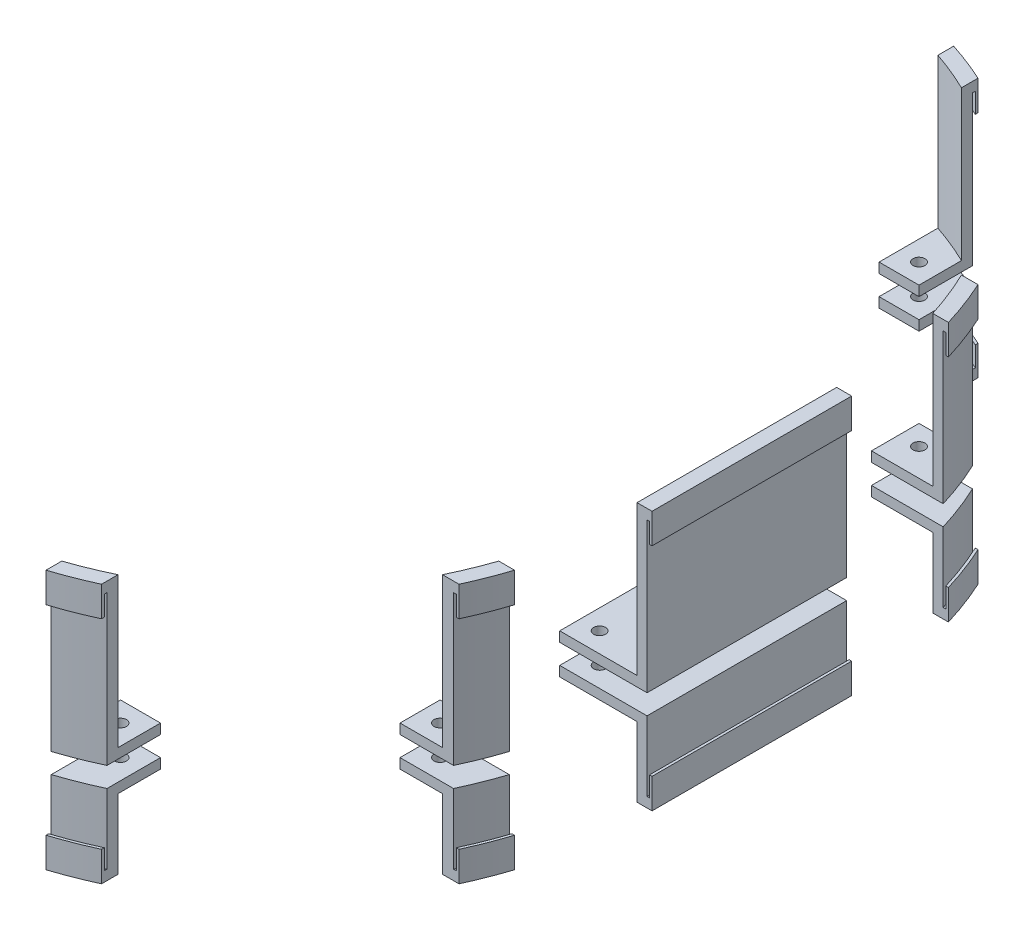
SolidWorks part; units mm, degrees
ref_plane "Front Plane" through (0, 0, 0) normal (0, 0, 1) x (1, 0, 0)
ref_plane "Top Plane" through (0, 0, 0) normal (0, 1, 0) x (1, 0, 0)
ref_plane "Right Plane" through (0, 0, 0) normal (1, 0, 0) x (0, 0, -1)
sketch "Sketch1" plane through (0, 0, 0) normal (0, 1, 0) x (1, 0, 0)
  line L1 (-34.1312, -148.4312) -> (34.1313, -148.4312)
  line L2 (-148.4312, -34.1312) -> (-148.4312, 34.1313)
  line L3 (-34.1312, 148.4313) -> (34.1313, 148.4313)
  line L4 (148.4312, -34.1312) -> (148.4312, 34.1313)
  line L5 (-148.4312, -148.4312) -> (148.4313, 148.4312) construction
  line L6 (-148.4312, 148.4312) -> (148.4313, -148.4312) construction
  arc A1 (-34.1312, -148.4312) -> (-148.4312, -34.1312) centre (-34.1312, -34.1312) cw
  arc A2 (34.1313, -148.4312) -> (148.4312, -34.1312) centre (34.1313, -34.1312) ccw
  arc A3 (34.1313, 148.4313) -> (148.4312, 34.1313) centre (34.1313, 34.1313) cw
  arc A4 (-148.4312, 34.1313) -> (-34.1312, 148.4313) centre (-34.1312, 34.1313) cw
  point P0 (0, 0)
  dimension "D1" = 296.8625
  dimension "D3" = 114.3
  dimension "D2" = 296.8625
extrude "Boss-Extrude1" add sketch "Sketch1" along normal blind 6.35
sketch "Sketch4" plane through (0, 6.35, 0) normal (0, 1, 0) x (1, 0, 0)
  line L0 (-39.448, -144.217) -> (39.448, -144.217)
  line L1 (-39.448, -120.2902) -> (39.448, -120.2902)
  line L2 (-39.448, 120.2902) -> (39.448, 120.2902)
  line L3 (-39.448, 144.217) -> (39.448, 144.217)
  line L4 (-39.448, 118.7027) -> (39.448, 118.7027)
  line L5 (-39.448, 145.8045) -> (39.448, 145.8045)
  line L6 (-39.448, -145.8045) -> (39.448, -145.8045)
  line L7 (-39.448, -118.7027) -> (39.448, -118.7027)
  line L8 (-13.125, 107.0625) -> (-13.125, 100.3125) construction
  line L9 (-13.125, 100.3125) -> (-18.875, 100.3125) construction
  line L10 (-18.875, 100.3125) -> (-18.875, 107.0625) construction
  line L11 (-18.875, 107.0625) -> (-13.125, 107.0625) construction
  line L12 (18.875, 107.0625) -> (18.875, 100.3125) construction
  line L13 (18.875, 100.3125) -> (13.125, 100.3125) construction
  line L14 (13.125, 100.3125) -> (13.125, 107.0625) construction
  line L15 (13.125, 107.0625) -> (18.875, 107.0625) construction
  line L16 (-7, 56.325) -> (-13, 56.325) construction
  line L17 (-13, 56.325) -> (-13, 64.325) construction
  line L18 (-13, 64.325) -> (-7, 64.325) construction
  line L19 (-7, 64.325) -> (-7, 56.325) construction
  line L20 (25, 56.325) -> (19, 56.325) construction
  line L21 (19, 56.325) -> (19, 64.325) construction
  line L22 (19, 64.325) -> (25, 64.325) construction
  line L23 (25, 64.325) -> (25, 56.325) construction
  line L24 (-13, -56.325) -> (-7, -56.325) construction
  line L25 (-7, -56.325) -> (-7, -64.325) construction
  line L26 (-7, -64.325) -> (-13, -64.325) construction
  line L27 (-13, -64.325) -> (-13, -56.325) construction
  line L28 (19, -56.325) -> (25, -56.325) construction
  line L29 (25, -56.325) -> (25, -64.325) construction
  line L30 (25, -64.325) -> (19, -64.325) construction
  line L31 (19, -64.325) -> (19, -56.325) construction
  line L32 (-18.875, -107.0625) -> (-18.875, -100.3125) construction
  line L33 (-18.875, -100.3125) -> (-13.125, -100.3125) construction
  line L34 (-13.125, -100.3125) -> (-13.125, -107.0625) construction
  line L35 (-13.125, -107.0625) -> (-18.875, -107.0625) construction
  line L36 (13.125, -107.0625) -> (13.125, -100.3125) construction
  line L37 (13.125, -100.3125) -> (18.875, -100.3125) construction
  line L38 (18.875, -100.3125) -> (18.875, -107.0625) construction
  line L39 (18.875, -107.0625) -> (13.125, -107.0625) construction
  line L40 (-13.125, 107.0625) -> (-13.125, 100.3125)
  line L41 (-13.125, 100.3125) -> (-18.875, 100.3125)
  line L42 (-18.875, 100.3125) -> (-18.875, 107.0625)
  line L43 (-18.875, 107.0625) -> (-13.125, 107.0625)
  line L44 (18.875, 107.0625) -> (18.875, 100.3125)
  line L45 (18.875, 100.3125) -> (13.125, 100.3125)
  line L46 (13.125, 100.3125) -> (13.125, 107.0625)
  line L47 (13.125, 107.0625) -> (18.875, 107.0625)
  line L48 (-7, 56.325) -> (-13, 56.325)
  line L49 (-13, 56.325) -> (-13, 64.325)
  line L50 (-13, 64.325) -> (-7, 64.325)
  line L51 (-7, 64.325) -> (-7, 56.325)
  line L52 (25, 56.325) -> (19, 56.325)
  line L53 (19, 56.325) -> (19, 64.325)
  line L54 (19, 64.325) -> (25, 64.325)
  line L55 (25, 64.325) -> (25, 56.325)
  line L56 (-13, -56.325) -> (-7, -56.325)
  line L57 (-7, -56.325) -> (-7, -64.325)
  line L58 (-7, -64.325) -> (-13, -64.325)
  line L59 (-13, -64.325) -> (-13, -56.325)
  line L60 (19, -56.325) -> (25, -56.325)
  line L61 (25, -56.325) -> (25, -64.325)
  line L62 (25, -64.325) -> (19, -64.325)
  line L63 (19, -64.325) -> (19, -56.325)
  line L64 (-18.875, -107.0625) -> (-18.875, -100.3125)
  line L65 (-18.875, -100.3125) -> (-13.125, -100.3125)
  line L66 (-13.125, -100.3125) -> (-13.125, -107.0625)
  line L67 (-13.125, -107.0625) -> (-18.875, -107.0625)
  line L68 (13.125, -107.0625) -> (13.125, -100.3125)
  line L69 (13.125, -100.3125) -> (18.875, -100.3125)
  line L70 (18.875, -100.3125) -> (18.875, -107.0625)
  line L71 (18.875, -107.0625) -> (13.125, -107.0625)
  line L72 (-18.875, -107.0625) -> (-13.125, -100.3125) construction
  line L73 (13.125, -107.0625) -> (18.875, -100.3125) construction
  line L74 (-13, -64.325) -> (-7, -56.325) construction
  line L75 (19, -64.325) -> (25, -56.325) construction
  line L76 (-13, 56.325) -> (-7, 64.325) construction
  line L77 (19, 56.325) -> (25, 64.325) construction
  line L78 (13.125, 100.3125) -> (18.875, 107.0625) construction
  line L79 (-18.875, 100.3125) -> (-13.125, 107.0625) construction
  arc A0 (58.6792, -125.8296) -> (39.448, -120.2902) centre (39.448, -156.4424) ccw construction
  arc A1 (58.6792, -138.6776) -> (58.6792, -125.8296) centre (54.6436, -132.2536) ccw construction
  arc A2 (39.448, -144.217) -> (58.6792, -138.6776) centre (39.448, -108.0647) ccw construction
  arc A3 (-39.448, -120.2902) -> (-58.6792, -125.8296) centre (-39.448, -156.4424) ccw construction
  arc A4 (-58.6792, -125.8296) -> (-58.6792, -138.6776) centre (-54.6436, -132.2536) ccw construction
  arc A5 (-58.6792, -138.6776) -> (-39.448, -144.217) centre (-39.448, -108.0647) ccw construction
  arc A6 (-58.6792, 125.8296) -> (-39.448, 120.2902) centre (-39.448, 156.4424) ccw construction
  arc A7 (-58.6792, 138.6776) -> (-58.6792, 125.8296) centre (-54.6436, 132.2536) ccw construction
  arc A8 (-39.448, 144.217) -> (-58.6792, 138.6776) centre (-39.448, 108.0647) ccw construction
  arc A9 (58.6792, 138.6776) -> (39.448, 144.217) centre (39.448, 108.0647) ccw construction
  arc A10 (58.6792, 125.8296) -> (58.6792, 138.6776) centre (54.6436, 132.2536) ccw construction
  arc A11 (39.448, 120.2902) -> (58.6792, 125.8296) centre (39.448, 156.4424) ccw construction
  arc A12 (58.6792, -125.8296) -> (39.448, -120.2902) centre (39.448, -156.4424) ccw
  arc A13 (58.6792, -138.6776) -> (58.6792, -125.8296) centre (54.6436, -132.2536) ccw
  arc A14 (39.448, -144.217) -> (58.6792, -138.6776) centre (39.448, -108.0647) ccw
  arc A15 (-39.448, -120.2902) -> (-58.6792, -125.8296) centre (-39.448, -156.4424) ccw
  arc A16 (-58.6792, -125.8296) -> (-58.6792, -138.6776) centre (-54.6436, -132.2536) ccw
  arc A17 (-58.6792, -138.6776) -> (-39.448, -144.217) centre (-39.448, -108.0647) ccw
  arc A18 (-58.6792, 125.8296) -> (-39.448, 120.2902) centre (-39.448, 156.4424) ccw
  arc A19 (-58.6792, 138.6776) -> (-58.6792, 125.8296) centre (-54.6436, 132.2536) ccw
  arc A20 (-39.448, 144.217) -> (-58.6792, 138.6776) centre (-39.448, 108.0647) ccw
  arc A21 (58.6792, 138.6776) -> (39.448, 144.217) centre (39.448, 108.0647) ccw
  arc A22 (58.6792, 125.8296) -> (58.6792, 138.6776) centre (54.6436, 132.2536) ccw
  arc A23 (39.448, 120.2902) -> (58.6792, 125.8296) centre (39.448, 156.4424) ccw
  arc A24 (-59.5236, 124.4853) -> (-39.448, 118.7027) centre (-39.448, 156.4424) ccw
  arc A25 (39.448, 118.7027) -> (59.5236, 124.4853) centre (39.448, 156.4424) ccw
  arc A26 (59.5236, 124.4853) -> (59.5236, 140.0219) centre (54.6436, 132.2536) ccw
  arc A27 (59.5236, 140.0219) -> (39.448, 145.8045) centre (39.448, 108.0647) ccw
  arc A28 (-39.448, 145.8045) -> (-59.5236, 140.0219) centre (-39.448, 108.0647) ccw
  arc A29 (-59.5236, 140.0219) -> (-59.5236, 124.4853) centre (-54.6436, 132.2536) ccw
  arc A30 (39.448, -145.8045) -> (59.5236, -140.0219) centre (39.448, -108.0647) ccw
  arc A31 (59.5236, -140.0219) -> (59.5236, -124.4853) centre (54.6436, -132.2536) ccw
  arc A32 (59.5236, -124.4853) -> (39.448, -118.7027) centre (39.448, -156.4424) ccw
  arc A33 (-39.448, -118.7027) -> (-59.5236, -124.4853) centre (-39.448, -156.4424) ccw
  arc A34 (-59.5236, -124.4853) -> (-59.5236, -140.0219) centre (-54.6436, -132.2536) ccw
  arc A35 (-59.5236, -140.0219) -> (-39.448, -145.8045) centre (-39.448, -108.0647) ccw
  point P58 (-16, -103.6875)
  point P60 (16, 103.6875)
  point P62 (-16, 103.6875)
  point P63 (-10, 60.325)
  point P66 (22, 60.325)
  point P68 (-10, -60.325)
  point P70 (16, -103.6875)
  point P71 (22, -60.325)
  dimension "D1" = 1.5875
extrude "Cut-Extrude1" cut sketch "Sketch4" against normal blind 6.35 contours L2 A23 A22 A21 L3 A20 A19 A18 | A28 A29 A24 L4 A25 A26 A27 L5 A23 L2 A18 A19 A20 L3 A21 A22 | A16 A17 L0 A14 A13 A12 L1 A15 | A34 A35 L6 A30 A31 A32 L7 A33 A17 A16 A15 L1 A12 A13 A14 L0
hole_wizard "M4 Clearance Hole1" positions "Sketch7" profile "Sketch9" hole size "M4" standard "ANSI Metric" end condition through all
sketch "Sketch7" plane through (0, 6.35, 0) normal (0, 1, 0) x (1, 0, 0)
  point P0 (-16, -103.6875)
  point P3 (16, -103.6875)
  point P6 (22, -60.325)
  point P9 (-10, -60.325)
  point P12 (-10, 60.325)
  point P15 (22, 60.325)
  point P18 (16, 103.6875)
  point P21 (-16, 103.6875)
sketch "Sketch9" plane through (-16, 6.35, 103.6875) normal (1, 0, 0) x (0, 0, 1)
  line L0 (0, 0) -> (0, 6.35)
  line L1 (0, 6.35) -> (2.25, 6.35)
  line L2 (2.25, 6.35) -> (2.25, 0)
  line L5 (2.25, 0) -> (0, 0)
  line L11 (0, -6.35) -> (0, 107.95) construction
  dimension "Thru Hole Dia." = 4.5
  dimension "Thru Hole Depth" = 6.35
sketch "Sketch11" plane through (0, 6.35, 0) normal (0, 1, 0) x (1, 0, 0)
  line L1 (101.6, 101.6) -> (-101.6, 101.6)
  line L2 (101.6, 101.6) -> (101.6, -101.6)
  line L3 (101.6, -101.6) -> (-101.6, -101.6)
  line L4 (-101.6, 101.6) -> (-101.6, -101.6)
  line L5 (101.6, 101.6) -> (-101.6, -101.6) construction
  line L6 (101.6, -101.6) -> (-101.6, 101.6) construction
  circle A0 centre (0, 0) radius 143.6841 construction
  point P7 (-127, -101.6)
  point P10 (-127, 101.6)
  point P11 (-127, -76.2)
  point P12 (-127, -50.8)
  point P13 (-127, -25.4)
  point P14 (-127, 0)
  point P15 (-127, 25.4)
  point P16 (-127, 50.8)
  point P17 (-127, 76.2)
  point P18 (-101.6, -101.6)
  point P19 (-101.6, 101.6)
  point P20 (-101.6, -76.2)
  point P21 (-101.6, -50.8)
  point P22 (-101.6, -25.4)
  point P23 (-101.6, 0)
  point P24 (-101.6, 25.4)
  point P25 (-101.6, 50.8)
  point P26 (-101.6, 76.2)
  point P27 (-76.2, -101.6)
  point P28 (-76.2, 101.6)
  point P29 (-76.2, -76.2)
  point P30 (-76.2, -50.8)
  point P31 (-76.2, -25.4)
  point P32 (-76.2, 0)
  point P33 (-76.2, 25.4)
  point P34 (-76.2, 50.8)
  point P35 (-76.2, 76.2)
  point P36 (-50.8, -101.6)
  point P37 (-50.8, 101.6)
  point P38 (-50.8, -76.2)
  point P39 (-50.8, -50.8)
  point P40 (-50.8, -25.4)
  point P41 (-50.8, 0)
  point P42 (-50.8, 25.4)
  point P43 (-50.8, 50.8)
  point P44 (-50.8, 76.2)
  point P45 (-25.4, -101.6)
  point P46 (-25.4, 101.6)
  point P47 (-25.4, -76.2)
  point P48 (-25.4, -50.8)
  point P49 (-25.4, -25.4)
  point P50 (-25.4, 0)
  point P51 (-25.4, 25.4)
  point P52 (-25.4, 50.8)
  point P53 (-25.4, 76.2)
  point P54 (0, -101.6)
  point P55 (0, 101.6)
  point P56 (0, -76.2)
  point P57 (0, -50.8)
  point P58 (0, -25.4)
  point P59 (0, 0)
  point P60 (0, 25.4)
  point P61 (0, 50.8)
  point P62 (0, 76.2)
  point P63 (25.4, -101.6)
  point P64 (25.4, 101.6)
  point P65 (25.4, -76.2)
  point P66 (25.4, -50.8)
  point P67 (25.4, -25.4)
  point P68 (25.4, 0)
  point P69 (25.4, 25.4)
  point P70 (25.4, 50.8)
  point P71 (25.4, 76.2)
  point P72 (50.8, -101.6)
  point P73 (50.8, 101.6)
  point P74 (50.8, -76.2)
  point P75 (50.8, -50.8)
  point P76 (50.8, -25.4)
  point P77 (50.8, 0)
  point P78 (50.8, 25.4)
  point P79 (50.8, 50.8)
  point P80 (50.8, 76.2)
  point P81 (76.2, -101.6)
  point P82 (76.2, 101.6)
  point P83 (76.2, -76.2)
  point P84 (76.2, -50.8)
  point P85 (76.2, -25.4)
  point P86 (76.2, 0)
  point P87 (76.2, 25.4)
  point P88 (76.2, 50.8)
  point P89 (76.2, 76.2)
  point P90 (101.6, -101.6)
  point P91 (101.6, 101.6)
  point P92 (101.6, -76.2)
  point P93 (101.6, -50.8)
  point P94 (101.6, -25.4)
  point P95 (101.6, 0)
  point P96 (101.6, 25.4)
  point P97 (101.6, 50.8)
  point P98 (101.6, 76.2)
  point P99 (127, -101.6)
  point P100 (127, 101.6)
  point P101 (127, -76.2)
  point P102 (127, -50.8)
  point P103 (127, -25.4)
  point P104 (127, 0)
  point P105 (127, 25.4)
  point P106 (127, 50.8)
  point P107 (127, 76.2)
  dimension "D1" = 203.2
  dimension "D2" = 25.4
  dimension "D3" = 11
  dimension "D4" = 9
hole_wizard "#6 Clearance Hole1" positions "Sketch12" profile "Sketch13" hole size "#6" standard "ANSI Inch" end condition through all
sketch "Sketch12" plane through (0, 6.35, 0) normal (0, 1, 0) x (1, 0, 0)
  point P0 (-101.6, -101.6)
  point P3 (-101.6, 101.6)
  point P6 (101.6, 101.6)
  point P9 (101.6, -101.6)
  point P12 (-127, -76.2)
  point P15 (-127, -50.8)
  point P18 (-127, 50.8)
  point P21 (-127, 76.2)
  point P24 (-101.6, 76.2)
  point P27 (-101.6, 50.8)
  point P30 (-101.6, 25.4)
  point P33 (-101.6, 0)
  point P36 (-101.6, -25.4)
  point P39 (-101.6, -50.8)
  point P42 (-101.6, -76.2)
  point P45 (-76.2, -101.6)
  point P48 (-50.8, -101.6)
  point P51 (-50.8, -76.2)
  point P54 (-76.2, -76.2)
  point P57 (-76.2, -50.8)
  point P60 (-50.8, -50.8)
  point P63 (-50.8, -25.4)
  point P66 (-76.2, -25.4)
  point P69 (-76.2, 0)
  point P72 (-50.8, 0)
  point P75 (-50.8, 25.4)
  point P78 (-76.2, 25.4)
  point P81 (-76.2, 50.8)
  point P84 (-50.8, 50.8)
  point P87 (-50.8, 76.2)
  point P90 (-76.2, 76.2)
  point P93 (-76.2, 101.6)
  point P96 (-50.8, 101.6)
  point P99 (50.8, -101.6)
  point P102 (76.2, -101.6)
  point P105 (101.6, -76.2)
  point P108 (127, -76.2)
  point P111 (127, -50.8)
  point P114 (101.6, -25.4)
  point P117 (101.6, -50.8)
  point P120 (76.2, -25.4)
  point P123 (76.2, -50.8)
  point P126 (76.2, -76.2)
  point P129 (50.8, -76.2)
  point P132 (50.8, -50.8)
  point P135 (50.8, -25.4)
  point P138 (50.8, 0)
  point P141 (76.2, 0)
  point P144 (101.6, 0)
  point P147 (101.6, 25.4)
  point P150 (101.6, 50.8)
  point P153 (101.6, 76.2)
  point P156 (127, 50.8)
  point P159 (127, 76.2)
  point P162 (76.2, 101.6)
  point P165 (50.8, 101.6)
  point P168 (50.8, 76.2)
  point P171 (76.2, 76.2)
  point P174 (76.2, 50.8)
  point P177 (76.2, 25.4)
  point P180 (50.8, 25.4)
  point P183 (50.8, 50.8)
  point P186 (0, 0)
  point P189 (-25.4, -25.4)
  point P192 (-25.4, 0)
  point P195 (-25.4, 25.4)
  point P198 (0, 25.4)
  point P201 (25.4, 25.4)
  point P204 (25.4, 0)
  point P207 (25.4, -25.4)
  point P210 (0, -25.4)
  point P213 (127, -25.4)
  point P216 (127, 0)
  point P219 (127, 25.4)
  point P222 (-127, -25.4)
  point P225 (-127, 0)
  point P228 (-127, 25.4)
sketch "Sketch13" plane through (-101.6, 6.35, 101.6) normal (1, 0, 0) x (0, 0, 1)
  line L0 (0, 0) -> (0, 6.35)
  line L1 (0, 6.35) -> (1.8986, 6.35)
  line L2 (1.8986, 6.35) -> (1.8986, 0)
  line L5 (1.8986, 0) -> (0, 0)
  line L11 (0, -6.35) -> (0, 107.95) construction
  dimension "Thru Hole Dia." = 3.7973
  dimension "Thru Hole Depth" = 6.35
sketch "Sketch14" plane through (0, 6.35, 0) normal (0, 1, 0) x (1, 0, 0)
  line L1 (76.2, -127) -> (-76.2, -127)
  line L2 (76.2, -127) -> (76.2, 127)
  line L3 (76.2, 127) -> (-76.2, 127)
  line L4 (-76.2, -127) -> (-76.2, 127)
  line L5 (76.2, -127) -> (-76.2, 127) construction
  line L6 (76.2, 127) -> (-76.2, -127) construction
  circle A1 centre (-76.2, -101.6) radius 1.8986 construction
  circle A2 centre (-101.6, -101.6) radius 1.8986 construction
  point P0 (0, 0)
  dimension "D1" = 25.4
  dimension "D2" = 25.4
hole_wizard "#6 Clearance Hole2" positions "Sketch15" profile "Sketch16" hole size "#6" standard "ANSI Inch" end condition through all
sketch "Sketch15" plane through (0, 6.35, 0) normal (0, 1, 0) x (1, 0, 0)
  point P0 (-76.2, -127)
  point P3 (76.2, -127)
  point P6 (76.2, 127)
  point P9 (-76.2, 127)
sketch "Sketch16" plane through (-76.2, 6.35, 127) normal (1, 0, 0) x (0, 0, 1)
  line L0 (0, 0) -> (0, 6.35)
  line L1 (0, 6.35) -> (1.8986, 6.35)
  line L2 (1.8986, 6.35) -> (1.8986, 0)
  line L5 (1.8986, 0) -> (0, 0)
  line L11 (0, -6.35) -> (0, 107.95) construction
  dimension "Thru Hole Dia." = 3.7973
  dimension "Thru Hole Depth" = 6.35
sketch "Sketch17" plane through (0, 6.35, 0) normal (0, 1, 0) x (1, 0, 0)
  line L0 (148.4313, -34.1312) -> (148.4312, 34.1313) construction
  line L1 (148.4313, -34.1312) -> (148.4312, 34.1313)
  line L2 (143.4746, 67.4257) -> (120.65, 67.4257)
  line L3 (148.4312, -31.75) -> (120.65, -31.75)
  line L4 (148.4312, -31.75) -> (148.4312, 31.75)
  line L5 (148.4312, 31.75) -> (120.65, 31.75)
  line L6 (120.65, -31.75) -> (120.65, 31.75)
  line L7 (120.65, 67.4257) -> (120.65, 82.55)
  line L8 (120.65, 82.55) -> (137.6692, 82.55)
  line L9 (82.55, 120.65) -> (69.85, 120.65)
  line L10 (69.85, 120.65) -> (69.85, 142.7068)
  line L11 (82.55, 120.65) -> (82.55, 137.6692)
  line L12 (69.85, -142.7068) -> (69.85, -120.65)
  line L13 (69.85, -120.65) -> (82.55, -120.65)
  line L14 (82.55, -120.65) -> (82.55, -137.6692)
  line L15 (137.6692, -82.55) -> (120.65, -82.55)
  line L16 (120.65, -82.55) -> (120.65, -69.85)
  line L17 (120.65, -69.85) -> (142.7068, -69.85)
  line L26 (-148.4312, 34.1313) -> (-148.4312, -34.1312)
  line L27 (34.1313, 148.4313) -> (-34.1312, 148.4313)
  line L28 (148.4313, -34.1312) -> (148.4312, 34.1313)
  line L29 (-34.1312, -148.4312) -> (34.1313, -148.4312)
  line L30 (-148.4312, 34.1313) -> (-148.4312, -34.1312)
  line L31 (34.1313, 148.4313) -> (-34.1312, 148.4313)
  line L32 (148.4313, -34.1312) -> (148.4312, 34.1313)
  line L33 (-34.1312, -148.4312) -> (34.1313, -148.4312)
  circle A0 centre (76.2, 127) radius 1.8987 construction
  circle A1 centre (127, 76.2) radius 1.8987 construction
  circle A2 centre (127, 0) radius 1.8986 construction
  circle A3 centre (127, 25.4) radius 1.8987 construction
  circle A4 centre (127, -25.4) radius 1.8986 construction
  circle A5 centre (127, -76.2) radius 1.8986 construction
  circle A6 centre (76.2, -127) radius 1.8987 construction
  arc A7 (148.4312, 34.1313) -> (34.1313, 148.4313) centre (34.1313, 34.1313) ccw construction
  arc A8 (34.1313, -148.4312) -> (148.4313, -34.1312) centre (34.1313, -34.1312) ccw construction
  circle A9 centre (76.2, 127) radius 1.8987
  circle A10 centre (127, 76.2) radius 1.8987
  circle A11 centre (127, 0) radius 1.8986
  circle A12 centre (127, 25.4) radius 1.8987
  circle A13 centre (127, -25.4) radius 1.8986
  circle A14 centre (127, -76.2) radius 1.8986
  circle A15 centre (76.2, -127) radius 1.8987
  arc A16 (143.4746, 67.4257) -> (137.6692, 82.55) centre (34.1313, 34.1313) ccw
  arc A17 (69.85, -142.7068) -> (82.55, -137.6692) centre (34.1313, -34.1312) ccw
  arc A18 (137.6692, -82.55) -> (142.7068, -69.85) centre (34.1313, -34.1312) ccw
  arc A19 (82.55, 137.6692) -> (69.85, 142.7068) centre (34.1313, 34.1313) ccw
  arc A28 (-148.4312, -34.1312) -> (-34.1312, -148.4312) centre (-34.1312, -34.1312) ccw
  arc A29 (-34.1312, 148.4313) -> (-148.4312, 34.1313) centre (-34.1312, 34.1313) ccw
  arc A30 (148.4312, 34.1313) -> (34.1313, 148.4313) centre (34.1313, 34.1313) ccw
  arc A31 (34.1313, -148.4312) -> (148.4313, -34.1312) centre (34.1313, -34.1312) ccw
  arc A32 (-148.4312, -34.1312) -> (-34.1312, -148.4312) centre (-34.1312, -34.1312) ccw
  arc A33 (-34.1312, 148.4313) -> (-148.4312, 34.1313) centre (-34.1312, 34.1313) ccw
  arc A34 (148.4312, 34.1313) -> (34.1313, 148.4313) centre (34.1313, 34.1313) ccw
  arc A35 (34.1313, -148.4312) -> (148.4313, -34.1312) centre (34.1313, -34.1312) ccw
  dimension "D1" = 6.35
  dimension "D2" = 6.35
  dimension "D3" = 6.35
  dimension "D4" = 6.35
  dimension "D5" = 6.35
  dimension "D6" = 6.35
  dimension "D7" = 6.35
  dimension "D8" = 6.35
  dimension "D9" = 6.35
  dimension "D10" = 6.35
  dimension "D11" = 6.35
  dimension "D12" = 8.7743
  dimension "D13" = 6.35
  dimension "D14" = 6.35
  dimension "D15" = 6.35
  dimension "D16" = 0
sketch "Sketch18" plane through (0, 0, 0) normal (0, -1, 0) x (1, 0, 0)
  line L4 (-148.4312, 34.1312) -> (-148.4312, -34.1312)
  line L5 (-34.1312, -148.4313) -> (34.1313, -148.4313)
  line L6 (148.4313, -34.1313) -> (148.4313, 34.1312)
  line L7 (34.1313, 148.4312) -> (-34.1312, 148.4312)
  line L8 (-148.4312, 34.1312) -> (-148.4312, -34.1312)
  line L9 (-34.1312, -148.4313) -> (34.1313, -148.4313)
  line L10 (148.4313, -34.1313) -> (148.4313, 34.1312)
  line L11 (34.1313, 148.4312) -> (-34.1312, 148.4312)
  arc A4 (-34.1312, 148.4312) -> (-148.4312, 34.1312) centre (-34.1312, 34.1312) ccw
  arc A5 (-148.4312, -34.1312) -> (-34.1312, -148.4313) centre (-34.1312, -34.1313) ccw
  arc A6 (34.1313, -148.4313) -> (148.4313, -34.1313) centre (34.1313, -34.1313) ccw
  arc A7 (148.4313, 34.1312) -> (34.1313, 148.4312) centre (34.1313, 34.1312) ccw
  arc A8 (-34.1312, 148.4312) -> (-148.4312, 34.1312) centre (-34.1312, 34.1312) ccw
  arc A9 (-148.4312, -34.1312) -> (-34.1312, -148.4313) centre (-34.1312, -34.1313) ccw
  arc A10 (34.1313, -148.4313) -> (148.4313, -34.1313) centre (34.1313, -34.1313) ccw
  arc A11 (148.4313, 34.1312) -> (34.1313, 148.4312) centre (34.1313, 34.1312) ccw
  dimension "D1" = 0
extrude "Boss-Extrude2" add sketch "Sketch17" along normal blind 3.175 contours L12 A17 L14 L13 A15 | L15 A18 L17 L16 A14 | L6 L3 L1 L5 A13 A12 A11 | L2 A16 L8 L7 A10 | L11 A19 L10 L9 A9
ref_plane "Plane1" through (0, 3.175, 0) normal (0, 1, 0) x (1, 0, 0)
mirror "Mirror3" about plane through (0, 3.175, 0) normal (0, 1, 0) of "Boss-Extrude2"
extrude "Cut-Extrude4" cut sketch "Sketch18" against normal blind 6.35
sketch "Sketch19" plane through (0, 9.525, 0) normal (0, 1, 0) x (1, 0, 0)
  line L0 (82.55, 120.65) -> (82.55, 137.6692) construction
  line L1 (69.85, 142.7068) -> (69.85, 120.65) construction
  line L4 (120.65, -31.75) -> (148.4313, -31.75) construction
  line L5 (148.4313, -31.75) -> (148.4313, 31.75) construction
  line L6 (148.4313, 31.75) -> (120.65, 31.75) construction
  line L7 (120.65, 67.4257) -> (143.4746, 67.4257) construction
  line L8 (137.6692, 82.55) -> (120.65, 82.55) construction
  line L10 (120.65, -82.55) -> (137.6692, -82.55) construction
  line L11 (142.7068, -69.85) -> (120.65, -69.85) construction
  line L13 (69.85, -120.65) -> (69.85, -142.7068) construction
  line L14 (82.55, -137.6692) -> (82.55, -120.65) construction
  line L16 (82.55, 134.1532) -> (82.55, 137.6692)
  line L17 (69.85, 142.7068) -> (69.85, 139.3593)
  line L20 (145.2562, -31.75) -> (148.4313, -31.75)
  line L21 (148.4313, -31.75) -> (148.4313, 31.75)
  line L22 (148.4313, 31.75) -> (145.2562, 31.75)
  line L23 (140.1513, 67.4257) -> (143.4746, 67.4257)
  line L24 (137.6692, 82.55) -> (134.1532, 82.55)
  line L26 (134.1532, -82.55) -> (137.6692, -82.55)
  line L27 (142.7068, -69.85) -> (139.3593, -69.85)
  line L29 (69.85, -139.3593) -> (69.85, -142.7068)
  line L30 (82.55, -137.6692) -> (82.55, -134.1532)
  line L32 (145.2562, -31.75) -> (145.2562, 31.75)
  arc A0 (82.55, 137.6692) -> (69.85, 142.7068) centre (34.1313, 34.1313) ccw construction
  arc A1 (143.4746, 67.4257) -> (137.6692, 82.55) centre (34.1313, 34.1313) ccw construction
  arc A2 (137.6692, -82.55) -> (142.7068, -69.85) centre (34.1313, -34.1312) ccw construction
  arc A3 (69.85, -142.7068) -> (82.55, -137.6692) centre (34.1313, -34.1312) ccw construction
  arc A4 (82.55, 137.6692) -> (69.85, 142.7068) centre (34.1313, 34.1313) ccw
  arc A5 (143.4746, 67.4257) -> (137.6692, 82.55) centre (34.1313, 34.1313) ccw
  arc A6 (137.6692, -82.55) -> (142.7068, -69.85) centre (34.1313, -34.1312) ccw
  arc A7 (69.85, -142.7068) -> (82.55, -137.6692) centre (34.1313, -34.1312) ccw
  arc A8 (69.85, -139.3593) -> (82.55, -134.1532) centre (34.1313, -34.1312) ccw
  arc A9 (140.1513, 67.4257) -> (134.1532, 82.55) centre (34.1313, 34.1313) ccw
  arc A10 (134.1532, -82.55) -> (139.3593, -69.85) centre (34.1313, -34.1312) ccw
  arc A11 (82.55, 134.1532) -> (69.85, 139.3593) centre (34.1313, 34.1313) ccw
  dimension "D1" = 3.175
  dimension "D2" = 3.175
  dimension "D3" = 3.175
sketch "Sketch22" plane through (0, -3.175, 0) normal (0, -1, 0) x (1, 0, 0)
  line L2 (137.6692, 82.55) -> (134.1532, 82.55)
  line L3 (139.3593, 69.85) -> (142.7068, 69.85)
  line L4 (137.6692, 82.55) -> (134.1532, 82.55)
  line L5 (139.3593, 69.85) -> (142.7068, 69.85)
  line L6 (143.4746, -67.4257) -> (140.1513, -67.4257)
  line L7 (134.1532, -82.55) -> (137.6692, -82.55)
  line L8 (143.4746, -67.4257) -> (140.1513, -67.4257)
  line L9 (134.1532, -82.55) -> (137.6692, -82.55)
  line L10 (82.55, -137.6692) -> (82.55, -134.1532)
  line L11 (69.85, -139.3593) -> (69.85, -142.7068)
  line L12 (148.4313, 31.75) -> (145.2562, 31.75)
  line L13 (148.4313, -31.75) -> (148.4313, 31.75)
  line L14 (145.2562, -31.75) -> (148.4313, -31.75)
  line L15 (145.2562, 31.75) -> (145.2562, -31.75)
  line L16 (148.4313, 31.75) -> (145.2562, 31.75)
  line L17 (148.4313, -31.75) -> (148.4313, 31.75)
  line L18 (145.2562, -31.75) -> (148.4313, -31.75)
  line L19 (145.2562, 31.75) -> (145.2562, -31.75)
  line L20 (82.55, -137.6692) -> (82.55, -134.1532)
  line L21 (69.85, -139.3593) -> (69.85, -142.7068)
  line L22 (69.85, 142.7068) -> (69.85, 139.3593)
  line L23 (82.55, 134.1532) -> (82.55, 137.6692)
  line L24 (69.85, 142.7068) -> (69.85, 139.3593)
  line L25 (82.55, 134.1532) -> (82.55, 137.6692)
  arc A2 (139.3593, 69.85) -> (134.1532, 82.55) centre (34.1313, 34.1312) ccw
  arc A3 (142.7068, 69.85) -> (137.6692, 82.55) centre (34.1313, 34.1312) ccw
  arc A4 (139.3593, 69.85) -> (134.1532, 82.55) centre (34.1313, 34.1312) ccw
  arc A5 (142.7068, 69.85) -> (137.6692, 82.55) centre (34.1313, 34.1312) ccw
  arc A6 (134.1532, -82.55) -> (140.1513, -67.4257) centre (34.1313, -34.1313) ccw
  arc A7 (137.6692, -82.55) -> (143.4746, -67.4257) centre (34.1313, -34.1313) ccw
  arc A8 (134.1532, -82.55) -> (140.1513, -67.4257) centre (34.1313, -34.1313) ccw
  arc A9 (137.6692, -82.55) -> (143.4746, -67.4257) centre (34.1313, -34.1313) ccw
  arc A10 (69.85, -142.7068) -> (82.55, -137.6692) centre (34.1313, -34.1313) ccw
  arc A11 (69.85, -139.3593) -> (82.55, -134.1532) centre (34.1313, -34.1313) ccw
  arc A12 (69.85, -142.7068) -> (82.55, -137.6692) centre (34.1313, -34.1313) ccw
  arc A13 (69.85, -139.3593) -> (82.55, -134.1532) centre (34.1313, -34.1313) ccw
  arc A14 (82.55, 134.1532) -> (69.85, 139.3593) centre (34.1313, 34.1312) ccw
  arc A15 (82.55, 137.6692) -> (69.85, 142.7068) centre (34.1313, 34.1312) ccw
  arc A16 (82.55, 134.1532) -> (69.85, 139.3593) centre (34.1313, 34.1312) ccw
  arc A17 (82.55, 137.6692) -> (69.85, 142.7068) centre (34.1313, 34.1312) ccw
  dimension "D1" = 0
  dimension "D2" = 0
  dimension "D3" = 0
  dimension "D4" = 0
  dimension "D5" = 0
extrude "Boss-Extrude3" add sketch "Sketch19" along normal blind 44.45
extrude "Boss-Extrude4" add sketch "Sketch22" along normal blind 19.05
sketch "Sketch23" plane through (0, 53.975, 0) normal (0, 1, 0) x (1, 0, 0)
  line L0 (140.1513, 67.4257) -> (143.4746, 67.4257) construction
  line L1 (137.6692, 82.55) -> (134.1532, 82.55) construction
  line L2 (69.85, 142.7068) -> (69.85, 139.3593) construction
  line L3 (82.55, 134.1532) -> (82.55, 137.6692) construction
  line L4 (148.4313, -31.75) -> (148.4313, 31.75) construction
  line L5 (148.4313, 31.75) -> (145.2562, 31.75) construction
  line L6 (145.2562, 31.75) -> (145.2562, -31.75) construction
  line L7 (145.2562, -31.75) -> (148.4313, -31.75) construction
  line L8 (134.1532, -82.55) -> (137.6692, -82.55) construction
  line L9 (142.7068, -69.85) -> (139.3593, -69.85) construction
  line L10 (69.85, -139.3593) -> (69.85, -142.7068) construction
  line L11 (82.55, -137.6692) -> (82.55, -134.1532) construction
  line L12 (140.1513, 67.4257) -> (143.4746, 67.4257)
  line L13 (137.6692, 82.55) -> (134.1532, 82.55)
  line L14 (69.85, 142.7068) -> (69.85, 139.3593)
  line L15 (82.55, 134.1532) -> (82.55, 137.6692)
  line L16 (148.4313, -31.75) -> (148.4313, 31.75)
  line L17 (148.4313, 31.75) -> (145.2562, 31.75)
  line L18 (145.2562, 31.75) -> (145.2562, -31.75)
  line L19 (145.2562, -31.75) -> (148.4313, -31.75)
  line L20 (134.1532, -82.55) -> (137.6692, -82.55)
  line L21 (142.7068, -69.85) -> (139.3593, -69.85)
  line L22 (69.85, -139.3593) -> (69.85, -142.7068)
  line L23 (82.55, -137.6692) -> (82.55, -134.1532)
  line L24 (150.0188, -31.75) -> (150.0188, 31.75)
  line L25 (150.0188, -31.75) -> (148.4313, -31.75)
  line L26 (148.4313, 31.75) -> (150.0188, 31.75)
  line L27 (69.85, -142.7068) -> (69.85, -144.3768)
  line L28 (82.55, -137.6692) -> (82.55, -139.4191)
  line L29 (137.6692, -82.55) -> (139.4191, -82.55)
  line L30 (142.7068, -69.85) -> (144.3768, -69.85)
  line L31 (69.85, 142.7068) -> (69.85, 144.3768)
  line L32 (82.55, 137.6692) -> (82.55, 139.4191)
  line L33 (137.6692, 82.55) -> (139.4191, 82.55)
  line L34 (143.4746, 67.4257) -> (145.133, 67.4257)
  arc A0 (140.1513, 67.4257) -> (134.1532, 82.55) centre (34.1313, 34.1313) ccw construction
  arc A1 (143.4746, 67.4257) -> (137.6692, 82.55) centre (34.1313, 34.1313) ccw construction
  arc A2 (82.55, 137.6692) -> (69.85, 142.7068) centre (34.1313, 34.1313) ccw construction
  arc A3 (82.55, 134.1532) -> (69.85, 139.3593) centre (34.1313, 34.1313) ccw construction
  arc A4 (134.1532, -82.55) -> (139.3593, -69.85) centre (34.1313, -34.1312) ccw construction
  arc A5 (137.6692, -82.55) -> (142.7068, -69.85) centre (34.1313, -34.1312) ccw construction
  arc A6 (69.85, -139.3593) -> (82.55, -134.1532) centre (34.1313, -34.1312) ccw construction
  arc A7 (69.85, -142.7068) -> (82.55, -137.6692) centre (34.1313, -34.1312) ccw construction
  arc A8 (140.1513, 67.4257) -> (134.1532, 82.55) centre (34.1313, 34.1313) ccw
  arc A9 (143.4746, 67.4257) -> (137.6692, 82.55) centre (34.1313, 34.1313) ccw
  arc A10 (82.55, 137.6692) -> (69.85, 142.7068) centre (34.1313, 34.1313) ccw
  arc A11 (82.55, 134.1532) -> (69.85, 139.3593) centre (34.1313, 34.1313) ccw
  arc A12 (134.1532, -82.55) -> (139.3593, -69.85) centre (34.1313, -34.1312) ccw
  arc A13 (137.6692, -82.55) -> (142.7068, -69.85) centre (34.1313, -34.1312) ccw
  arc A14 (69.85, -139.3593) -> (82.55, -134.1532) centre (34.1313, -34.1312) ccw
  arc A15 (69.85, -142.7068) -> (82.55, -137.6692) centre (34.1313, -34.1312) ccw
  arc A16 (69.85, -144.3768) -> (82.55, -139.4191) centre (34.1313, -34.1312) ccw
  arc A17 (145.133, 67.4257) -> (139.4191, 82.55) centre (34.1313, 34.1313) ccw
  arc A18 (139.4191, -82.55) -> (144.3768, -69.85) centre (34.1313, -34.1312) ccw
  arc A19 (82.55, 139.4191) -> (69.85, 144.3768) centre (34.1313, 34.1313) ccw
  arc M2 (82.55, -134.1532) -> (69.85, -139.3593) centre (34.1313, -34.1312) cw
  line M3 (69.85, -139.3593) -> (69.85, -142.7068)
  arc M4 (69.85, -142.7068) -> (82.55, -137.6692) centre (34.1313, -34.1312) ccw
  line M5 (82.55, -137.6692) -> (82.55, -134.1532)
  dimension "D2" = 1.5875
  dimension "D3" = 1.5875
  dimension "D1" = 1.5875
sketch "Sketch24" plane through (0, -22.225, 0) normal (0, -1, 0) x (1, 0, 0)
  line L0 (82.55, -134.1532) -> (82.55, -137.6692) construction
  line L1 (69.85, -142.7068) -> (69.85, -139.3593) construction
  line L2 (69.85, -142.7068) -> (69.85, -144.3768) construction
  line L3 (82.55, -137.6692) -> (82.55, -139.4191) construction
  line L4 (140.1513, -67.4257) -> (143.4746, -67.4257) construction
  line L5 (137.6692, -82.55) -> (134.1532, -82.55) construction
  line L6 (137.6692, -82.55) -> (139.4191, -82.55) construction
  line L7 (143.4746, -67.4257) -> (145.133, -67.4257) construction
  line L8 (148.4313, 31.75) -> (148.4313, -31.75) construction
  line L9 (148.4313, -31.75) -> (145.2562, -31.75) construction
  line L10 (145.2562, -31.75) -> (145.2562, 31.75) construction
  line L11 (145.2562, 31.75) -> (148.4313, 31.75) construction
  line L12 (148.4313, -31.75) -> (150.0188, -31.75) construction
  line L13 (150.0188, 31.75) -> (150.0188, -31.75) construction
  line L14 (150.0188, 31.75) -> (148.4313, 31.75) construction
  line L15 (69.85, 139.3593) -> (69.85, 142.7068) construction
  line L16 (82.55, 137.6692) -> (82.55, 134.1532) construction
  line L17 (69.85, 142.7068) -> (69.85, 144.3768) construction
  line L18 (82.55, 137.6692) -> (82.55, 139.4191) construction
  line L19 (134.1532, 82.55) -> (137.6692, 82.55) construction
  line L20 (142.7068, 69.85) -> (139.3593, 69.85) construction
  line L21 (137.6692, 82.55) -> (139.4191, 82.55) construction
  line L22 (142.7068, 69.85) -> (144.3768, 69.85) construction
  line L23 (82.55, -134.1532) -> (82.55, -137.6692)
  line L24 (69.85, -142.7068) -> (69.85, -139.3593)
  line L25 (69.85, -142.7068) -> (69.85, -144.3768)
  line L26 (82.55, -137.6692) -> (82.55, -139.4191)
  line L27 (140.1513, -67.4257) -> (143.4746, -67.4257)
  line L28 (137.6692, -82.55) -> (134.1532, -82.55)
  line L29 (137.6692, -82.55) -> (139.4191, -82.55)
  line L30 (143.4746, -67.4257) -> (145.133, -67.4257)
  line L31 (148.4313, 31.75) -> (148.4313, -31.75)
  line L32 (148.4313, -31.75) -> (145.2562, -31.75)
  line L33 (145.2562, -31.75) -> (145.2562, 31.75)
  line L34 (145.2562, 31.75) -> (148.4313, 31.75)
  line L35 (148.4313, -31.75) -> (150.0188, -31.75)
  line L36 (150.0188, 31.75) -> (150.0188, -31.75)
  line L37 (150.0188, 31.75) -> (148.4313, 31.75)
  line L38 (69.85, 139.3593) -> (69.85, 142.7068)
  line L39 (82.55, 137.6692) -> (82.55, 134.1532)
  line L40 (69.85, 142.7068) -> (69.85, 144.3768)
  line L41 (82.55, 137.6692) -> (82.55, 139.4191)
  line L42 (134.1532, 82.55) -> (137.6692, 82.55)
  line L43 (142.7068, 69.85) -> (139.3593, 69.85)
  line L44 (137.6692, 82.55) -> (139.4191, 82.55)
  line L45 (142.7068, 69.85) -> (144.3768, 69.85)
  arc A0 (69.85, -139.3593) -> (82.55, -134.1532) centre (34.1313, -34.1313) ccw construction
  arc A1 (69.85, -144.3768) -> (82.55, -139.4191) centre (34.1313, -34.1313) ccw construction
  arc A2 (69.85, -142.7068) -> (82.55, -137.6692) centre (34.1313, -34.1313) ccw construction
  arc A3 (134.1532, -82.55) -> (140.1513, -67.4257) centre (34.1313, -34.1313) ccw construction
  arc A4 (139.4191, -82.55) -> (145.133, -67.4257) centre (34.1313, -34.1313) ccw construction
  arc A5 (137.6692, -82.55) -> (143.4746, -67.4257) centre (34.1313, -34.1313) ccw construction
  arc A6 (82.55, 134.1532) -> (69.85, 139.3593) centre (34.1313, 34.1312) ccw construction
  arc A7 (82.55, 139.4191) -> (69.85, 144.3768) centre (34.1313, 34.1312) ccw construction
  arc A8 (82.55, 137.6692) -> (69.85, 142.7068) centre (34.1313, 34.1312) ccw construction
  arc A9 (139.3593, 69.85) -> (134.1532, 82.55) centre (34.1313, 34.1312) ccw construction
  arc A10 (144.3768, 69.85) -> (139.4191, 82.55) centre (34.1313, 34.1312) ccw construction
  arc A11 (142.7068, 69.85) -> (137.6692, 82.55) centre (34.1313, 34.1312) ccw construction
  arc A12 (69.85, -139.3593) -> (82.55, -134.1532) centre (34.1313, -34.1313) ccw
  arc A13 (69.85, -144.3768) -> (82.55, -139.4191) centre (34.1313, -34.1313) ccw
  arc A14 (69.85, -142.7068) -> (82.55, -137.6692) centre (34.1313, -34.1313) ccw
  arc A15 (134.1532, -82.55) -> (140.1513, -67.4257) centre (34.1313, -34.1313) ccw
  arc A16 (139.4191, -82.55) -> (145.133, -67.4257) centre (34.1313, -34.1313) ccw
  arc A17 (137.6692, -82.55) -> (143.4746, -67.4257) centre (34.1313, -34.1313) ccw
  arc A18 (82.55, 134.1532) -> (69.85, 139.3593) centre (34.1313, 34.1312) ccw
  arc A19 (82.55, 139.4191) -> (69.85, 144.3768) centre (34.1313, 34.1312) ccw
  arc A20 (82.55, 137.6692) -> (69.85, 142.7068) centre (34.1313, 34.1312) ccw
  arc A21 (139.3593, 69.85) -> (134.1532, 82.55) centre (34.1313, 34.1312) ccw
  arc A22 (144.3768, 69.85) -> (139.4191, 82.55) centre (34.1313, 34.1312) ccw
  arc A23 (142.7068, 69.85) -> (137.6692, 82.55) centre (34.1313, 34.1312) ccw
  line M1 (145.2562, 31.75) -> (145.2562, -31.75)
  line M2 (145.2562, -31.75) -> (148.4313, -31.75)
  line M3 (148.4313, -31.75) -> (148.4313, 31.75)
  line M4 (148.4313, 31.75) -> (145.2562, 31.75)
extrude "Boss-Extrude5" add sketch "Sketch23" along normal blind 3.175 contours L27 A16 L28 M4 | M5 M2 M3 M4 | L29 A18 L30 A13 | L20 A13 L21 A12 | L26 L16 L25 L24 | L18 L19 L16 L17 | L34 A17 L33 A9 | L12 A9 L13 A8 | A11 L15 A10 L14 | L32 A19 L31 A10
extrude "Boss-Extrude6" add sketch "Sketch24" along normal blind 3.175 contours A23 L45 A22 L44 | L43 A23 L42 A21 | L36 L37 L35 M3 | M4 M1 M2 M3 | A17 L29 A16 L30 | L28 A17 L27 A15 | A20 L41 A19 L40 | L39 A20 L38 A18 | L24 A14 L23 A12 | A14 L25 A13 L26
sketch "Sketch25" plane through (0, 53.975, 0) normal (0, -1, 0) x (1, 0, 0)
  line L0 (82.55, -139.4191) -> (82.55, -137.6692) construction
  line L1 (69.85, -142.7068) -> (69.85, -144.3768) construction
  line L2 (145.133, -67.4257) -> (143.4746, -67.4257) construction
  line L3 (137.6692, -82.55) -> (139.4191, -82.55) construction
  line L4 (150.0188, 31.75) -> (148.4313, 31.75) construction
  line L5 (148.4313, 31.75) -> (148.4313, -31.75) construction
  line L6 (148.4313, -31.75) -> (150.0188, -31.75) construction
  line L7 (150.0188, -31.75) -> (150.0188, 31.75) construction
  line L8 (139.4191, 82.55) -> (137.6692, 82.55) construction
  line L9 (142.7068, 69.85) -> (144.3768, 69.85) construction
  line L10 (69.85, 144.3768) -> (69.85, 142.7068) construction
  line L11 (82.55, 137.6692) -> (82.55, 139.4191) construction
  line L12 (82.55, -139.4191) -> (82.55, -137.6692)
  line L13 (69.85, -142.7068) -> (69.85, -144.3768)
  line L14 (145.133, -67.4257) -> (143.4746, -67.4257)
  line L15 (137.6692, -82.55) -> (139.4191, -82.55)
  line L16 (150.0188, 31.75) -> (148.4313, 31.75)
  line L17 (148.4313, 31.75) -> (148.4313, -31.75)
  line L18 (148.4313, -31.75) -> (150.0188, -31.75)
  line L19 (150.0188, -31.75) -> (150.0188, 31.75)
  line L20 (139.4191, 82.55) -> (137.6692, 82.55)
  line L21 (142.7068, 69.85) -> (144.3768, 69.85)
  line L22 (69.85, 144.3768) -> (69.85, 142.7068)
  line L23 (82.55, 137.6692) -> (82.55, 139.4191)
  line L24 (149.225, 31.75) -> (149.225, -31.75)
  arc A0 (69.85, -142.7068) -> (82.55, -137.6692) centre (34.1313, -34.1313) ccw construction
  arc A1 (69.85, -144.3768) -> (82.55, -139.4191) centre (34.1313, -34.1313) ccw construction
  arc A2 (137.6692, -82.55) -> (143.4746, -67.4257) centre (34.1313, -34.1313) ccw construction
  arc A3 (139.4191, -82.55) -> (145.133, -67.4257) centre (34.1313, -34.1313) ccw construction
  arc A4 (142.7068, 69.85) -> (137.6692, 82.55) centre (34.1313, 34.1312) ccw construction
  arc A5 (144.3768, 69.85) -> (139.4191, 82.55) centre (34.1313, 34.1312) ccw construction
  arc A6 (82.55, 137.6692) -> (69.85, 142.7068) centre (34.1313, 34.1312) ccw construction
  arc A7 (82.55, 139.4191) -> (69.85, 144.3768) centre (34.1313, 34.1312) ccw construction
  arc A8 (69.85, -142.7068) -> (82.55, -137.6692) centre (34.1313, -34.1313) ccw
  arc A9 (69.85, -144.3768) -> (82.55, -139.4191) centre (34.1313, -34.1313) ccw
  arc A10 (137.6692, -82.55) -> (143.4746, -67.4257) centre (34.1313, -34.1313) ccw
  arc A11 (139.4191, -82.55) -> (145.133, -67.4257) centre (34.1313, -34.1313) ccw
  arc A12 (142.7068, 69.85) -> (137.6692, 82.55) centre (34.1313, 34.1312) ccw
  arc A13 (144.3768, 69.85) -> (139.4191, 82.55) centre (34.1313, 34.1312) ccw
  arc A14 (82.55, 137.6692) -> (69.85, 142.7068) centre (34.1313, 34.1312) ccw
  arc A15 (82.55, 139.4191) -> (69.85, 144.3768) centre (34.1313, 34.1312) ccw
  arc A16 (149.2004, 31.75) -> (148.4312, 20.6375) centre (34.1313, 34.1312) ccw
  arc A17 (148.4312, -20.6375) -> (149.2004, -31.75) centre (34.1313, -34.1313) ccw
  line M2 (69.85, 144.3768) -> (69.85, 142.7068)
  arc M5 (82.55, 139.4191) -> (69.85, 144.3768) centre (34.1313, 34.1312) ccw
  dimension "D1" = 0.7937
  dimension "D2" = 0.7937
  dimension "D3" = 0.7937
extrude "Boss-Extrude8" add sketch "Sketch25" along normal blind 6.35 contours A17 L13 A9 L12 | A17 L15 A11 L14 | L16 L24 L18 L19 | A16 L21 A13 L20 | A16 L23 M5 M2
sketch "Sketch27" plane through (0, -22.225, 0) normal (0, 1, 0) x (1, 0, 0)
  line L0 (69.85, 143.5421) -> (69.85, 144.3768) construction
  line L1 (82.55, 139.4191) -> (82.55, 138.5448) construction
  line L2 (138.5448, 82.55) -> (139.4191, 82.55) construction
  line L3 (145.133, 67.4257) -> (144.3041, 67.4257) construction
  line L4 (150.0188, -31.75) -> (149.225, -31.75) construction
  line L5 (149.225, -31.75) -> (149.225, 31.75) construction
  line L6 (149.225, 31.75) -> (150.0188, 31.75) construction
  line L7 (150.0188, 31.75) -> (150.0188, -31.75) construction
  line L8 (143.5421, -69.85) -> (144.3768, -69.85) construction
  line L9 (139.4191, -82.55) -> (138.5448, -82.55) construction
  line L10 (82.55, -138.5448) -> (82.55, -139.4191) construction
  line L11 (69.85, -144.3768) -> (69.85, -143.5421) construction
  line L12 (69.85, 143.5421) -> (69.85, 144.3768)
  line L13 (82.55, 139.4191) -> (82.55, 138.5448)
  line L14 (138.5448, 82.55) -> (139.4191, 82.55)
  line L15 (145.133, 67.4257) -> (144.3041, 67.4257)
  line L16 (150.0188, -31.75) -> (149.225, -31.75)
  line L17 (149.225, -31.75) -> (149.225, 31.75)
  line L18 (149.225, 31.75) -> (150.0188, 31.75)
  line L19 (150.0188, 31.75) -> (150.0188, -31.75)
  line L20 (143.5421, -69.85) -> (144.3768, -69.85)
  line L21 (139.4191, -82.55) -> (138.5448, -82.55)
  line L22 (82.55, -138.5448) -> (82.55, -139.4191)
  line L23 (69.85, -144.3768) -> (69.85, -143.5421)
  arc A0 (82.55, 138.5448) -> (69.85, 143.5421) centre (34.1313, 34.1313) ccw construction
  arc A1 (82.55, 139.4191) -> (69.85, 144.3768) centre (34.1313, 34.1313) ccw construction
  arc A2 (144.3041, 67.4257) -> (138.5448, 82.55) centre (34.1313, 34.1313) ccw construction
  arc A3 (145.133, 67.4257) -> (139.4191, 82.55) centre (34.1313, 34.1313) ccw construction
  arc A4 (138.5448, -82.55) -> (143.5421, -69.85) centre (34.1313, -34.1312) ccw construction
  arc A5 (139.4191, -82.55) -> (144.3768, -69.85) centre (34.1313, -34.1312) ccw construction
  arc A6 (69.85, -143.5421) -> (82.55, -138.5448) centre (34.1313, -34.1312) ccw construction
  arc A7 (69.85, -144.3768) -> (82.55, -139.4191) centre (34.1313, -34.1312) ccw construction
  arc A8 (82.55, 138.5448) -> (69.85, 143.5421) centre (34.1313, 34.1313) ccw
  arc A9 (82.55, 139.4191) -> (69.85, 144.3768) centre (34.1313, 34.1313) ccw
  arc A10 (144.3041, 67.4257) -> (138.5448, 82.55) centre (34.1313, 34.1313) ccw
  arc A11 (145.133, 67.4257) -> (139.4191, 82.55) centre (34.1313, 34.1313) ccw
  arc A12 (138.5448, -82.55) -> (143.5421, -69.85) centre (34.1313, -34.1312) ccw
  arc A13 (139.4191, -82.55) -> (144.3768, -69.85) centre (34.1313, -34.1312) ccw
  arc A14 (69.85, -143.5421) -> (82.55, -138.5448) centre (34.1313, -34.1312) ccw
  arc A15 (69.85, -144.3768) -> (82.55, -139.4191) centre (34.1313, -34.1312) ccw
extrude "Boss-Extrude9" add sketch "Sketch27" along normal blind 6.35
sketch "Sketch28" plane through (150.0188, 0, 0) normal (1, 0, 0) x (0, 0, -1)
  line L1 (-157.7513, 82.653) -> (92.7874, 82.653)
  line L2 (-157.7513, 82.653) -> (-157.7513, -70.9441)
  line L3 (-157.7513, -70.9441) -> (92.7874, -70.9441)
  line L4 (92.7874, 82.653) -> (92.7874, -70.9441)
  line L5 (174.2974, 81.161) -> (190.159, 81.161)
  line L6 (174.2974, 81.161) -> (174.2974, -78.3944)
  line L7 (174.2974, -78.3944) -> (190.159, -78.3944)
  line L8 (190.159, 81.161) -> (190.159, -78.3944)
extrude "Cut-Extrude7" [suppressed] cut sketch "Sketch28" against normal through all both and the other way through all
